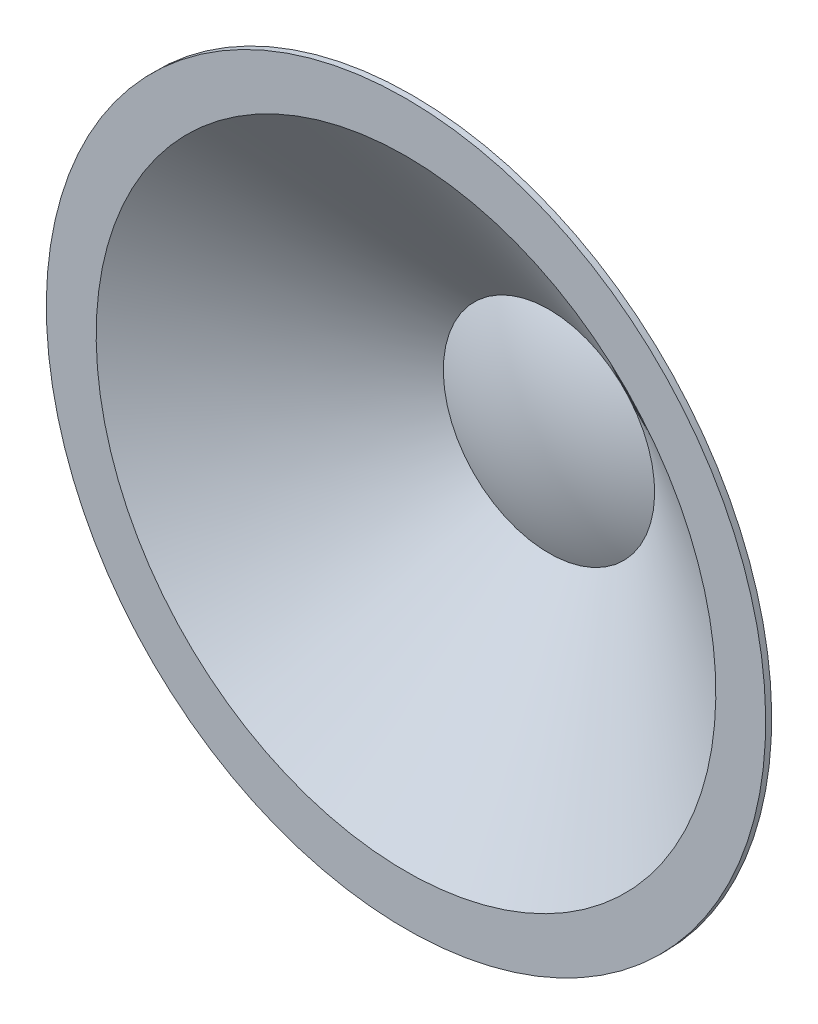
SolidWorks part; units mm, degrees
ref_plane "Front" through (0, 0, 0) normal (0, 0, 1) x (1, 0, 0)
ref_plane "Top" through (0, 0, 0) normal (0, 1, 0) x (1, 0, 0)
ref_plane "Right" through (0, 0, 0) normal (1, 0, 0) x (0, 0, -1)
other "Configuration Table"
sketch "Sketch1" plane through (0, 0, 0) normal (1, 0, 0) x (0, 0, -1)
  line L0 (0, 30) -> (0, 26)
  line L1 (0, 26) -> (12, 8.8622)
  line L2 (12, 8.8622) -> (12, 0) construction
  line L3 (12, 0) -> (0, 0) construction
  line L4 (10, 0) -> (10, -2.3819) construction
  arc A0 (12, 8.8622) -> (10, 0) centre (30.6348, 0) ccw
  dimension "D1" = 30
  dimension "D2" = 145
  dimension "D3" = 12
  dimension "D4" = 4
  dimension "D5" = 2
revolve "Revolve-Thin1" add sketch "Sketch1" angle 360 about L3
